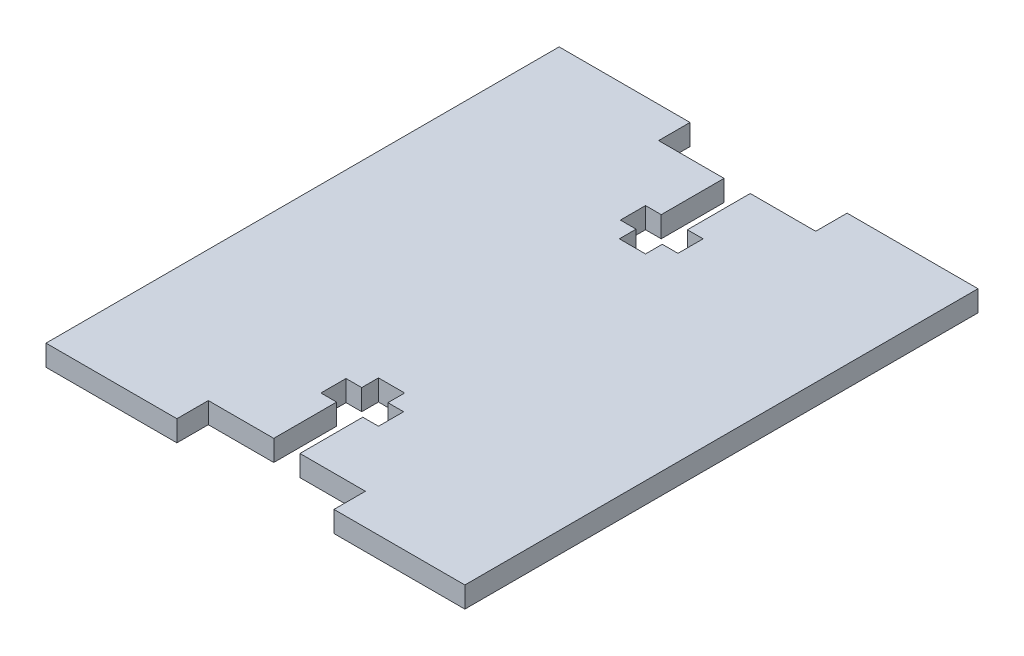
SolidWorks part; units mm, degrees
material "PVC rigido"
ref_plane "Piano frontale" through (0, 0, 0) normal (0, 0, 1) x (1, 0, 0)
ref_plane "Piano superiore" through (0, 0, 0) normal (0, 1, 0) x (1, 0, 0)
ref_plane "Piano destro" through (0, 0, 0) normal (1, 0, 0) x (0, 0, -1)
sketch "Schizzo1" plane through (0, 0, 0) normal (0, 1, 0) x (1, 0, 0)
  line L1 (-54.5649, -28.2811) -> (-14.5649, -28.2811)
  line L2 (-54.5649, -28.2811) -> (-54.5649, 20.7189)
  line L3 (-54.5649, 20.7189) -> (-14.5649, 20.7189)
  line L4 (-14.5649, -28.2811) -> (-14.5649, 20.7189)
  dimension "D1" = 40
  dimension "D2" = 49
sketch "Schizzo2" plane through (0, 0, 0) normal (0, 1, 0) x (1, 0, 0)
  line L0 (-54.5649, -3.7811) -> (-14.5649, -3.7811) construction
  line L5 (-54.5649, -28.2811) -> (-54.5649, 20.7189) construction
  line L6 (-14.5649, -28.2811) -> (-14.5649, 20.7189) construction
  line L7 (-34.5649, -28.2811) -> (-34.5649, 20.7189) construction
  line L8 (-54.5649, -28.2811) -> (-14.5649, -28.2811) construction
  line L9 (-54.5649, 20.7189) -> (-14.5649, 20.7189) construction
  line L22 (-42.0649, -28.2811) -> (-27.0649, -28.2811)
  line L23 (-42.0649, -28.2811) -> (-42.0649, -25.2811)
  line L24 (-42.0649, -25.2811) -> (-27.0649, -25.2811)
  line L25 (-27.0649, -28.2811) -> (-27.0649, -25.2811)
  line L26 (-42.0649, 20.7189) -> (-42.0649, 17.7189)
  line L27 (-42.0649, 17.7189) -> (-27.0649, 17.7189)
  line L28 (-27.0649, 20.7189) -> (-27.0649, 17.7189)
  line L29 (-42.0649, 20.7189) -> (-27.0649, 20.7189)
  point P33 (-34.5649, -25.2811)
  dimension "D3" = 15
  dimension "D4" = 3
extrude "Estrusione-Estrusione2" add sketch "Schizzo1" against normal blind 2
extrude "Taglio-Estrusione1" cut sketch "Schizzo2" against normal through all
sketch "Schizzo3" plane through (0, 0, 0) normal (0, 1, 0) x (1, 0, 0)
  line L1 (-35.8149, -25.2811) -> (-33.3149, -25.2811)
  line L2 (-54.5649, -3.7811) -> (-14.5649, -3.7811) construction
  line L3 (-54.5649, 20.7189) -> (-54.5649, -28.2811) construction
  line L15 (-14.5649, -28.2811) -> (-14.5649, 20.7189) construction
  line L19 (-34.5649, 17.7189) -> (-34.5649, -25.2811) construction
  line L20 (-42.0649, 17.7189) -> (-27.0649, 17.7189) construction
  line L21 (-27.0649, -25.2811) -> (-42.0649, -25.2811) construction
  line L26 (-35.8149, -25.2811) -> (-35.8149, -19.2811)
  line L27 (-35.8149, -19.2811) -> (-37.3149, -19.2811)
  line L28 (-37.3149, -19.2811) -> (-37.3149, -16.8811)
  line L29 (-37.3149, -16.8811) -> (-35.8149, -16.8811)
  line L30 (-35.8149, -16.8811) -> (-35.8149, -15.2811)
  line L31 (-35.8149, -15.2811) -> (-33.3149, -15.2811)
  line L32 (-33.3149, -15.2811) -> (-33.3149, -16.8811)
  line L33 (-33.3149, -16.8811) -> (-31.8149, -16.8811)
  line L34 (-31.8149, -16.8811) -> (-31.8149, -19.2811)
  line L35 (-31.8149, -19.2811) -> (-33.3149, -19.2811)
  line L36 (-33.3149, -19.2811) -> (-33.3149, -25.2811)
  line L60 (-35.8149, 7.7189) -> (-33.3149, 7.7189)
  line L61 (-35.8149, 9.3189) -> (-35.8149, 7.7189)
  line L62 (-37.3149, 9.3189) -> (-35.8149, 9.3189)
  line L63 (-37.3149, 11.7189) -> (-37.3149, 9.3189)
  line L64 (-35.8149, 11.7189) -> (-37.3149, 11.7189)
  line L65 (-35.8149, 17.7189) -> (-35.8149, 11.7189)
  line L66 (-35.8149, 17.7189) -> (-33.3149, 17.7189)
  line L67 (-33.3149, 11.7189) -> (-33.3149, 17.7189)
  line L68 (-31.8149, 11.7189) -> (-33.3149, 11.7189)
  line L69 (-31.8149, 9.3189) -> (-31.8149, 11.7189)
  line L70 (-33.3149, 9.3189) -> (-31.8149, 9.3189)
  line L71 (-33.3149, 7.7189) -> (-33.3149, 9.3189)
  point P53 (-34.5649, -25.2811)
  dimension "D2" = 10
  dimension "D3" = 5.5
  dimension "D8" = 2.5
  dimension "D9" = 6
  dimension "D11" = 2.4
extrude "Taglio-Estrusione3" cut sketch "Schizzo3" against normal through all
equation "\"Thickness2\"=2"
equation "\"Thickness3\"=3"
equation "\"D4@Schizzo2\"=\"Thickness3\""
equation "\"D1@Estrusione-Estrusione2\"=\"Thickness2\""
equation "\"D2@Schizzo1\"=\"Thickness2\"*2+45"
